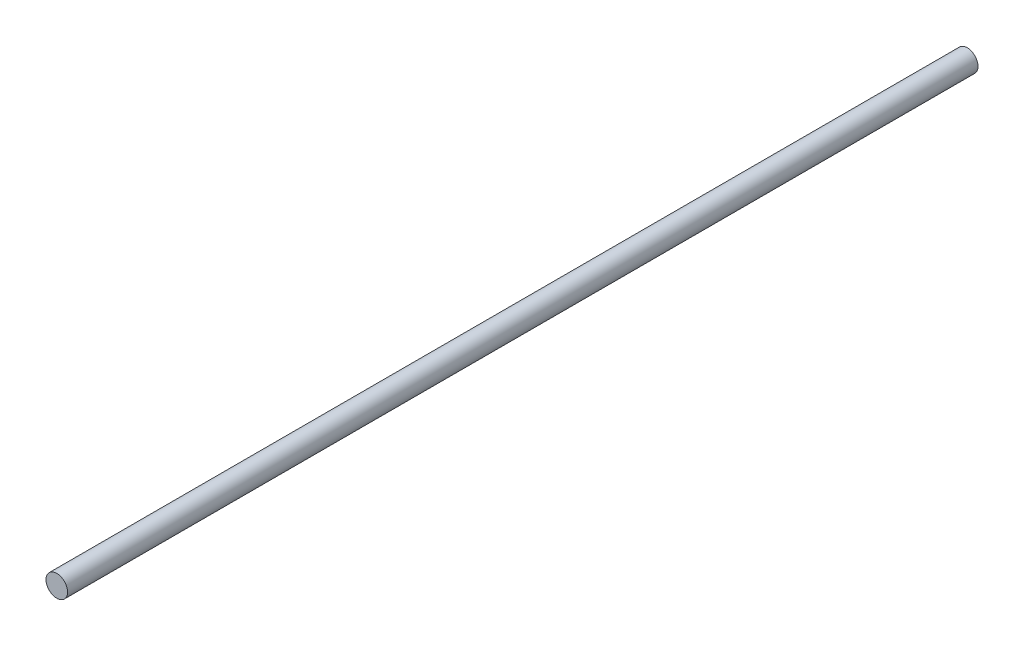
SolidWorks part; units mm, degrees
ref_plane "Front Plane" through (0, 0, 0) normal (0, 0, 1) x (1, 0, 0)
ref_plane "Top Plane" through (0, 0, 0) normal (0, 1, 0) x (1, 0, 0)
ref_plane "Right Plane" through (0, 0, 0) normal (1, 0, 0) x (0, 0, -1)
sketch "Sketch1" plane through (0, 0, 0) normal (0, 0, 1) x (1, 0, 0)
  circle A0 centre (0, 0) radius 6.35
  dimension "D1" = 12.7
extrude "Boss-Extrude1" add sketch "Sketch1" along normal mid plane 536
cosmetic thread "Cosmetic Thread1" parameters "D1"=44.5, "D2"=11.1887
cosmetic thread "Cosmetic Thread4" parameters "D1"=44.5, "D2"=11.1887
